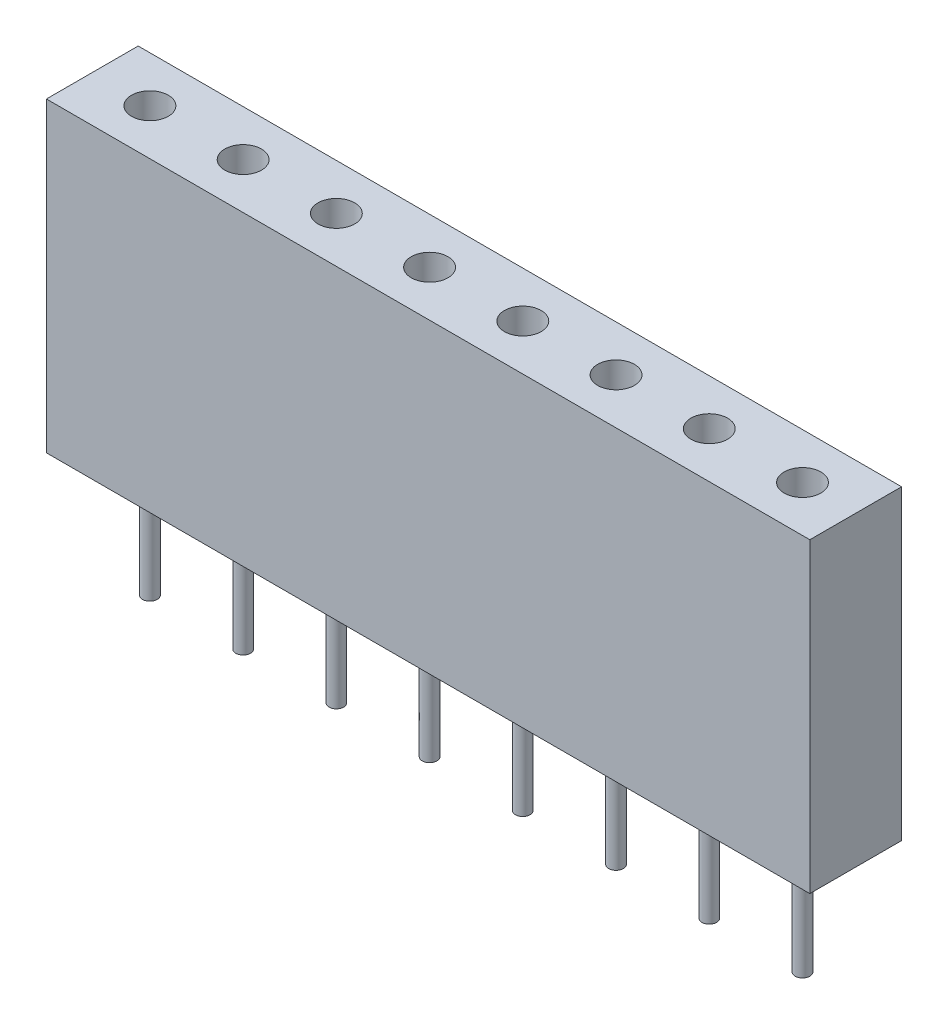
SolidWorks part; units mm, degrees
ref_plane "Front Plane" through (0, 0, 0) normal (0, 0, 1) x (1, 0, 0)
ref_plane "Top Plane" through (0, 0, 0) normal (0, 1, 0) x (1, 0, 0)
ref_plane "Right Plane" through (0, 0, 0) normal (1, 0, 0) x (0, 0, -1)
sketch "Sketch1" plane through (0, 0, 0) normal (0, 1, 0) x (1, 0, 0)
  line L1 (-10.4, -1.25) -> (10.4, -1.25)
  line L2 (-10.4, -1.25) -> (-10.4, 1.25)
  line L3 (-10.4, 1.25) -> (10.4, 1.25)
  line L4 (10.4, -1.25) -> (10.4, 1.25)
  line L5 (-10.4, -1.25) -> (10.4, 1.25) construction
  line L6 (-10.4, 1.25) -> (10.4, -1.25) construction
  point P0 (0, 0)
  dimension "D1" = 20.8
  dimension "D2" = 2.5
extrude "Boss-Extrude1" add sketch "Sketch1" along normal blind 8.35
sketch "Sketch2" plane through (0, 8.35, 0) normal (0, 1, 0) x (1, 0, 0)
  line L0 (-10.4, 0) -> (10.4, 0) construction
  line L1 (-10.4, 1.25) -> (-10.4, -1.25) construction
  line L2 (10.4, -1.25) -> (10.4, 1.25) construction
  circle A0 centre (-8.83, 0) radius 0.5
  dimension "D1" = 1
  dimension "D2" = 1.57
extrude "Cut-Extrude1" cut sketch "Sketch2" against normal blind 3
sketch "Sketch3" plane through (0, 0, 0) normal (0, -1, 0) x (1, 0, 0)
  line L0 (-10.4, -1.25) -> (-10.4, 1.25) construction
  circle A0 centre (-8.83, 0) radius 0.2
  dimension "D1" = 0.4
  dimension "D2" = 1.57
extrude "Boss-Extrude2" add sketch "Sketch3" along normal blind 3.2
pattern_linear "LPattern1" count 8 spacing 2.54 along (1, 0, 0) of "Cut-Extrude1", "Boss-Extrude2"
